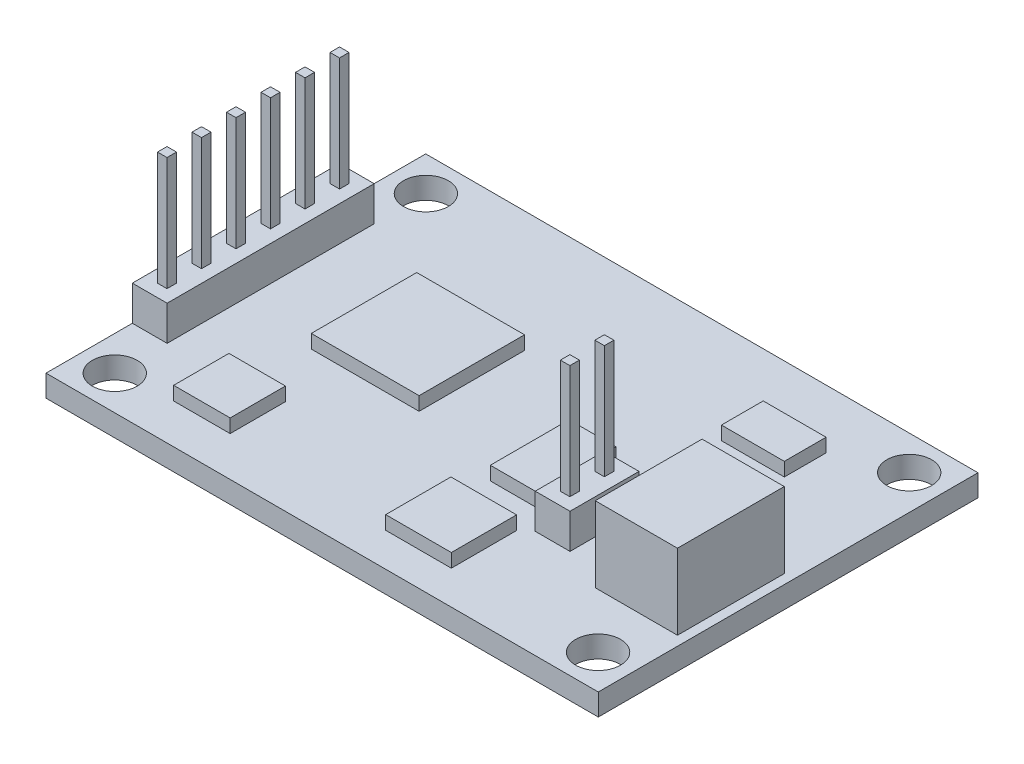
SolidWorks part; units mm, degrees
ref_plane "Front Plane" through (0, 0, 0) normal (0, 0, 1) x (1, 0, 0)
ref_plane "Top Plane" through (0, 0, 0) normal (0, 1, 0) x (1, 0, 0)
ref_plane "Right Plane" through (0, 0, 0) normal (1, 0, 0) x (0, 0, -1)
sketch "Sketch1" plane through (0, 0, 0) normal (0, 1, 0) x (1, 0, 0)
  line L0 (0, 13.975) -> (0, -13.975) construction
  line L1 (-20.325, 13.975) -> (20.325, 13.975)
  line L2 (-20.325, 13.975) -> (-20.325, -13.975)
  line L3 (-20.325, -13.975) -> (20.325, -13.975)
  line L4 (20.325, 13.975) -> (20.325, -13.975)
  line L5 (-20.325, 13.975) -> (20.325, -13.975) construction
  line L6 (-20.325, -13.975) -> (20.325, 13.975) construction
  line L7 (-20.325, 0) -> (20.325, 0) construction
  circle A0 centre (17.7875, 11.45) radius 1.65
  circle A1 centre (-17.7875, 11.45) radius 1.65
  circle A2 centre (17.7875, -11.45) radius 1.65
  circle A3 centre (-17.7875, -11.45) radius 1.65
  point P0 (0, 0)
  dimension "D3" = 3.3
  dimension "D1" = 40.65
  dimension "D2" = 27.95
  dimension "D4" = 35.575
  dimension "D5" = 22.9
extrude "Boss-Extrude1" add sketch "Sketch1" along normal blind 1.6
sketch "Sketch2" plane through (0, 1.6, 0) normal (0, 1, 0) x (1, 0, 0)
  line L0 (-20.325, 0) -> (20.325, 0) construction
  line L1 (-20.325, 13.975) -> (-20.325, -13.975) construction
  line L2 (20.325, -13.975) -> (20.325, 13.975) construction
  line L3 (-20.325, -13.975) -> (20.325, -13.975) construction
  line L4 (-20.325, 7.62) -> (-17.765, 7.62)
  line L5 (-20.325, 7.62) -> (-20.325, -7.62)
  line L6 (-20.325, -7.62) -> (-17.765, -7.62)
  line L7 (-17.765, 7.62) -> (-17.765, -7.62)
  line L8 (-20.325, 7.62) -> (-17.765, -7.62) construction
  line L9 (-20.325, -7.62) -> (-17.765, 7.62) construction
  line L10 (7.765, -0.975) -> (10.325, -0.975)
  line L11 (7.765, -0.975) -> (7.765, -6.055)
  line L12 (7.765, -6.055) -> (10.325, -6.055)
  line L13 (10.325, -0.975) -> (10.325, -6.055)
  point P6 (-19.045, 0)
  dimension "D1" = 2.56
  dimension "D2" = 15.24
  dimension "D3" = 5.08
  dimension "D4" = 7.92
  dimension "D5" = 10
extrude "Boss-Extrude2" add sketch "Sketch2" along normal blind 2.56 separate body
sketch "Sketch3" plane through (0, 4.16, 0) normal (0, 1, 0) x (1, 0, 0)
  line L0 (-19.045, 7.62) -> (-19.045, -7.62) construction
  line L1 (-17.765, 7.62) -> (-20.325, 7.62) construction
  line L2 (-20.325, -7.62) -> (-17.765, -7.62) construction
  line L3 (9.045, -0.975) -> (9.045, -6.055) construction
  line L4 (10.325, -0.975) -> (7.765, -0.975) construction
  line L5 (7.765, -6.055) -> (10.325, -6.055) construction
  line L6 (-19.395, 3.46) -> (-18.695, 3.46)
  line L7 (-19.395, 6.7) -> (-18.695, 6.7)
  line L8 (-19.395, 6.7) -> (-19.395, 6)
  line L9 (-19.395, 6) -> (-18.695, 6)
  line L10 (-18.695, 6.7) -> (-18.695, 6)
  line L11 (-19.395, 6.7) -> (-18.695, 6) construction
  line L12 (-19.395, 6) -> (-18.695, 6.7) construction
  line L13 (-18.695, 4.16) -> (-18.695, 3.46)
  line L14 (-19.395, 4.16) -> (-18.695, 4.16)
  line L15 (-19.395, 4.16) -> (-19.395, 3.46)
  line L16 (-19.395, 0.92) -> (-18.695, 0.92)
  line L17 (-18.695, 1.62) -> (-18.695, 0.92)
  line L18 (-19.395, 1.62) -> (-18.695, 1.62)
  line L19 (-19.395, 1.62) -> (-19.395, 0.92)
  line L20 (-19.395, -1.62) -> (-18.695, -1.62)
  line L21 (-18.695, -0.92) -> (-18.695, -1.62)
  line L22 (-19.395, -0.92) -> (-18.695, -0.92)
  line L23 (-19.395, -0.92) -> (-19.395, -1.62)
  line L24 (-19.395, -4.16) -> (-18.695, -4.16)
  line L25 (-18.695, -3.46) -> (-18.695, -4.16)
  line L26 (-19.395, -3.46) -> (-18.695, -3.46)
  line L27 (-19.395, -3.46) -> (-19.395, -4.16)
  line L28 (-19.395, -6.7) -> (-18.695, -6.7)
  line L29 (-18.695, -6) -> (-18.695, -6.7)
  line L30 (-19.395, -6) -> (-18.695, -6)
  line L31 (-19.395, -6) -> (-19.395, -6.7)
  line L32 (9.045, -2.245) -> (9.045, -0.975) construction
  line L33 (9.395, -1.895) -> (8.695, -1.895)
  line L34 (9.395, -1.895) -> (9.395, -2.595)
  line L35 (9.395, -2.595) -> (8.695, -2.595)
  line L36 (8.695, -1.895) -> (8.695, -2.595)
  line L37 (9.395, -1.895) -> (8.695, -2.595) construction
  line L38 (9.395, -2.595) -> (8.695, -1.895) construction
  line L39 (-19.045, 6.35) -> (-19.045, 7.62) construction
  line L40 (8.695, -4.435) -> (8.695, -5.135)
  line L41 (9.395, -5.135) -> (8.695, -5.135)
  line L42 (9.395, -4.435) -> (9.395, -5.135)
  line L43 (9.395, -4.435) -> (8.695, -4.435)
  line L44 (8.695, -1.895) -> (8.695, -4.435) construction
  line L45 (-19.395, 6.7) -> (-19.395, 4.16) construction
  point P12 (-19.045, 6.35)
  point P17 (9.045, -2.245)
  dimension "D1" = 0.7
  dimension "D2" = 1.27
  dimension "D4" = 2.54
  dimension "D3" = 6
  dimension "D5" = 2
extrude "Boss-Extrude3" add sketch "Sketch3" along normal blind 8.36
sketch "Sketch4" plane through (0, 1.6, 0) normal (0, 1, 0) x (1, 0, 0)
  line L1 (-12.0934, 5.0804) -> (-4.158, 5.0804)
  line L2 (-12.0934, 5.0804) -> (-12.0934, -2.6793)
  line L3 (-12.0934, -2.6793) -> (-4.158, -2.6793)
  line L4 (-4.158, 5.0804) -> (-4.158, -2.6793)
  line L5 (-13.8503, -6.9837) -> (-9.6923, -6.9837)
  line L6 (-13.8503, -6.9837) -> (-13.8503, -11.0539)
  line L7 (-13.8503, -11.0539) -> (-9.6923, -11.0539)
  line L8 (-9.6923, -6.9837) -> (-9.6923, -11.0539)
  line L9 (2.1961, -6.6909) -> (7.0276, -6.6909)
  line L10 (2.1961, -6.6909) -> (2.1961, -11.4931)
  line L11 (2.1961, -11.4931) -> (7.0276, -11.4931)
  line L12 (7.0276, -6.6909) -> (7.0276, -11.4931)
  line L13 (2.8989, 1.303) -> (6.3542, 1.303)
  line L14 (2.8989, 1.303) -> (2.8989, -4.4948)
  line L15 (2.8989, -4.4948) -> (6.3542, -4.4948)
  line L16 (6.3542, 1.303) -> (6.3542, -4.4948)
  line L17 (8.8431, 9.6484) -> (13.4696, 9.6484)
  line L18 (8.8431, 9.6484) -> (8.8431, 6.5738)
  line L19 (8.8431, 6.5738) -> (13.4696, 6.5738)
  line L20 (13.4696, 9.6484) -> (13.4696, 6.5738)
extrude "Boss-Extrude4" add sketch "Sketch4" along normal blind 1
sketch "Sketch5" plane through (0, 1.6, 0) normal (0, 1, 0) x (1, 0, 0)
  line L0 (10.325, -3.515) -> (20.325, -3.515) construction
  line L1 (10.325, -6.055) -> (10.325, -0.975) construction
  line L2 (20.325, -13.975) -> (20.325, 13.975) construction
  line L4 (13.575, 0.415) -> (19.625, 0.415)
  line L5 (13.575, 0.415) -> (13.575, -7.445)
  line L6 (13.575, -7.445) -> (19.625, -7.445)
  line L7 (19.625, 0.415) -> (19.625, -7.445)
  line L8 (13.575, 0.415) -> (19.625, -7.445) construction
  line L9 (13.575, -7.445) -> (19.625, 0.415) construction
  point P6 (16.6, -3.515)
  dimension "D1" = 7.86
  dimension "D2" = 6.05
  dimension "D3" = 0.7
extrude "Boss-Extrude5" add sketch "Sketch5" along normal blind 5.55
